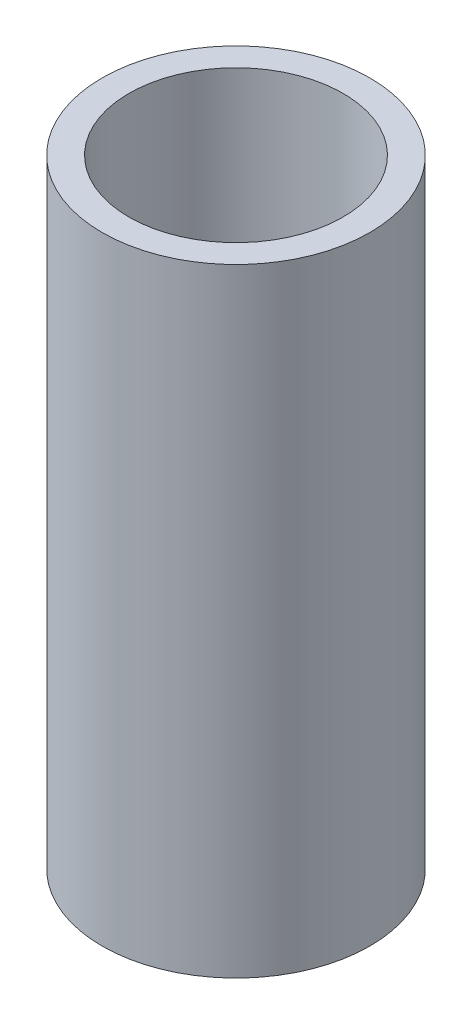
SolidWorks part; units mm, degrees
ref_plane "Front Plane" through (0, 0, 0) normal (0, 0, 1) x (1, 0, 0)
ref_plane "Top Plane" through (0, 0, 0) normal (0, 1, 0) x (1, 0, 0)
ref_plane "Right Plane" through (0, 0, 0) normal (1, 0, 0) x (0, 0, -1)
sketch "Sketch2" plane through (0, 0, 0) normal (0, 1, 0) x (1, 0, 0)
  circle A0 centre (0, 0) radius 3.25
  circle A1 centre (0, 0) radius 2.6
  dimension "D1" = 5.2
  dimension "D2" = 6.5
extrude "Boss-Extrude1" add sketch "Sketch2" along normal blind 15
